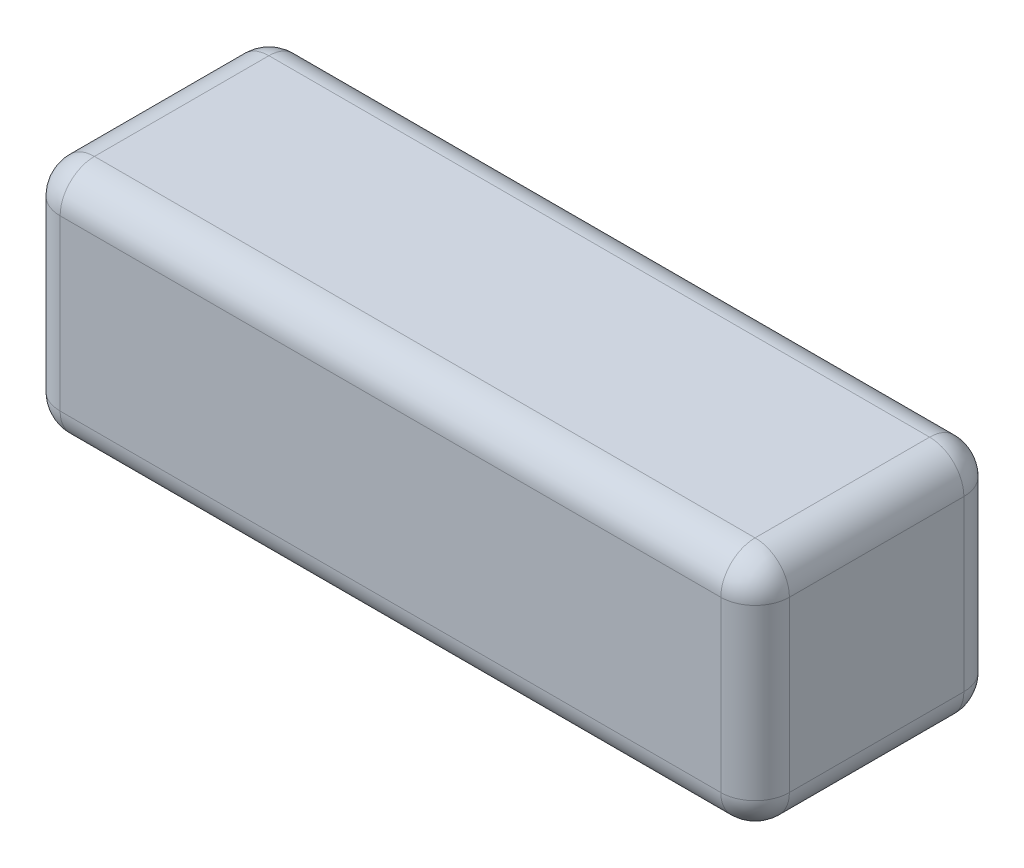
SolidWorks part; units mm, degrees
ref_plane "Front Plane" through (0, 0, 0) normal (0, 0, 1) x (1, 0, 0)
ref_plane "Top Plane" through (0, 0, 0) normal (0, 1, 0) x (1, 0, 0)
ref_plane "Right Plane" through (0, 0, 0) normal (1, 0, 0) x (0, 0, -1)
sketch "Sketch1" plane through (0, 0, 0) normal (0, 1, 0) x (1, 0, 0)
  line L1 (0, 0) -> (135, 0)
  line L2 (0, 0) -> (0, -45)
  line L3 (0, -45) -> (135, -45)
  line L4 (135, 0) -> (135, -45)
  dimension "D1" = 135
  dimension "D2" = 45
extrude "Boss-Extrude1" add sketch "Sketch1" along normal blind 44
fillet "Fillet1" radius 6.35 12 edges at (0, 22, 45) (135, 22, 45) (135, 22, 0) (0, 22, 0) (67.5, 44, 0) (135, 44, 22.5) (67.5, 44, 45) (0, 44, 22.5) (67.5, 0, 0) (135, 0, 22.5) (67.5, 0, 45) (0, 0, 22.5)
